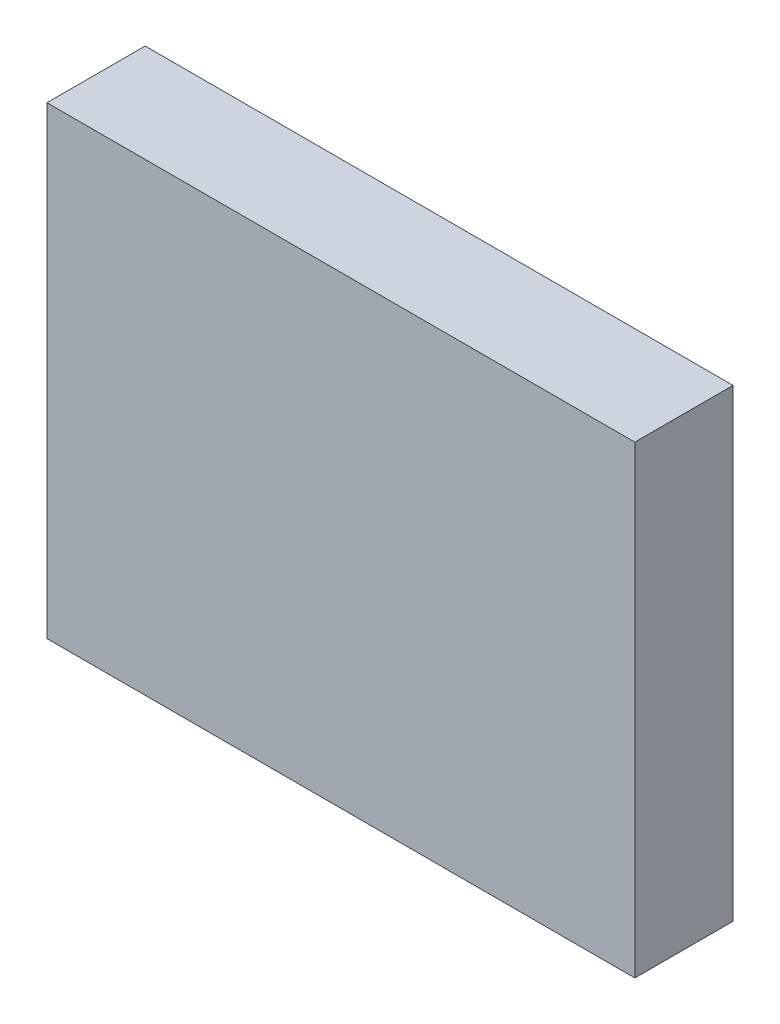
SolidWorks part; units mm, degrees
ref_plane "Alzado" through (0, 0, 0) normal (0, 0, 1) x (1, 0, 0)
ref_plane "Planta" through (0, 0, 0) normal (0, 1, 0) x (1, 0, 0)
ref_plane "Vista lateral" through (0, 0, 0) normal (1, 0, 0) x (0, 0, -1)
sketch "Croquis1" plane through (0, 0, 0) normal (0, 0, 1) x (1, 0, 0)
  line L1 (-19, -15) -> (19, -15)
  line L2 (-19, -15) -> (-19, 15)
  line L3 (-19, 15) -> (19, 15)
  line L4 (19, -15) -> (19, 15)
  line L5 (-19, -15) -> (19, 15) construction
  line L6 (-19, 15) -> (19, -15) construction
  point P0 (0, 0)
  dimension "D1" = 38
  dimension "D2" = 30
extrude "Saliente-Extruir1" add sketch "Croquis1" along normal blind 6.35
